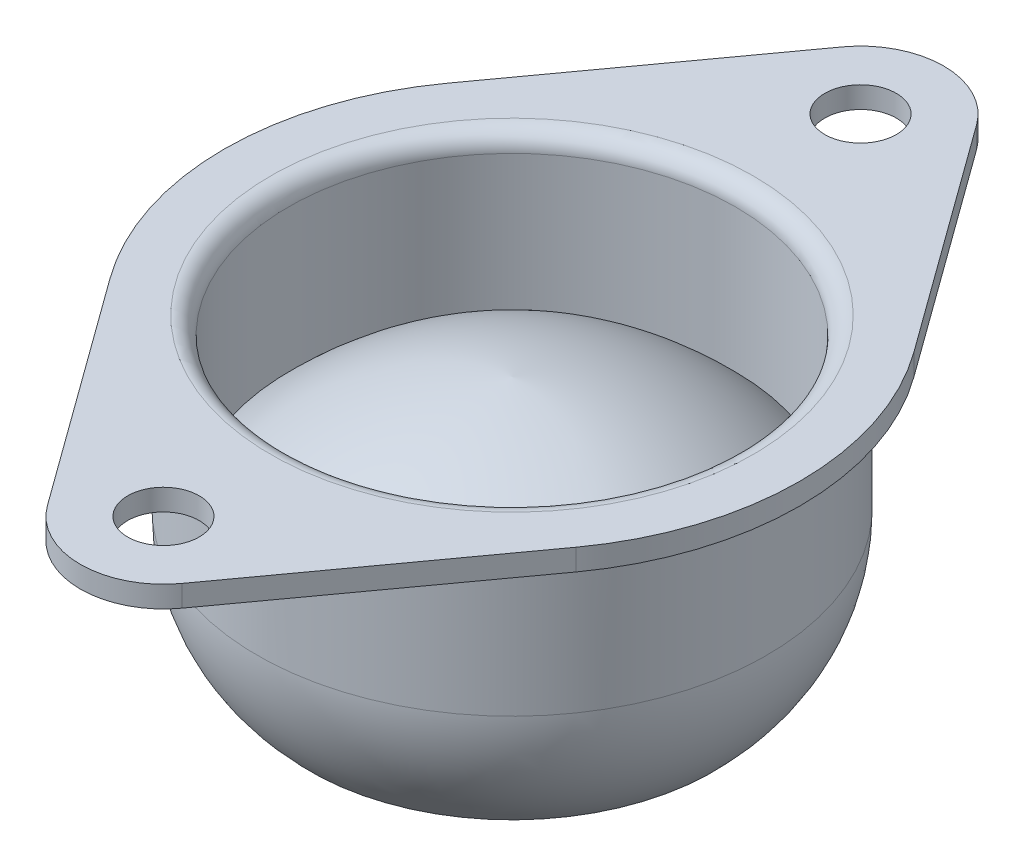
SolidWorks part; units mm, degrees
ref_plane "Plano frontal" through (0, 0, 0) normal (0, 0, 1) x (1, 0, 0)
ref_plane "Plano superior" through (0, 0, 0) normal (0, 1, 0) x (1, 0, 0)
ref_plane "Plano direito" through (0, 0, 0) normal (1, 0, 0) x (0, 0, -1)
sketch "Esboço1" plane through (0, 0, 0) normal (0, 0, 1) x (1, 0, 0)
  line L0 (0, 0) -> (0, 23844.2125) construction
  line L1 (0, 0) -> (-16.1, 0)
  line L2 (-16.1, 0) -> (-16.1, -1.2)
  line L3 (-16.1, -1.2) -> (-14.25, -1.2)
  line L4 (-14.25, -1.2) -> (-14.25, -9.3586)
  line L8 (0, 0) -> (0, -21)
  line L9 (0, -21) -> (9.18, -21) construction
  arc A3 (-14.25, -9.3586) -> (-11.25, -16.5) centre (-4.25, -9.3586) ccw
  arc A4 (-11.25, -16.5) -> (-7.5, -16) centre (-9.6827, -13.9419) ccw
  arc A5 (-7.5, -16) -> (0, -21) centre (0, -12.875) ccw
  dimension "D1" = 28.5
  dimension "D4" = 16.5
  dimension "D5" = 10
  dimension "D10" = 3
  dimension "D2" = 21
  dimension "D3" = 32.2
  dimension "D6" = 22.5
  dimension "D7" = 1.2
  dimension "D8" = 15
  dimension "D9" = 5
revolve "Revolução1" add sketch "Esboço1" angle 360 about L0
sketch "Esboço2" plane through (0, 0, 0) normal (0, 1, 0) x (1, 0, 0)
  line L0 (0, -19.5) -> (0, 19.5) construction
  line L1 (3.764, 22.2304) -> (13.0323, 9.4536)
  line L2 (-16.1, 0) -> (16.1, 0) construction
  line L3 (-3.764, 22.2304) -> (-13.0323, 9.4536)
  line L4 (3.764, -22.2304) -> (13.0323, -9.4536)
  line L5 (-3.764, -22.2304) -> (-13.0323, -9.4536)
  circle A2 centre (0, 0) radius 16.1 construction
  circle A3 centre (0, 0) radius 16.1
  circle A4 centre (0, -19.5) radius 2
  circle A5 centre (0, 19.5) radius 2
  arc A6 (3.764, 22.2304) -> (-3.764, 22.2304) centre (0, 19.5) ccw
  arc A7 (-3.764, -22.2304) -> (3.764, -22.2304) centre (0, -19.5) ccw
  point P0 (0, 24.15)
  point P4 (0, 0)
  point P6 (0, -24.15)
  point P15 (0, 0)
  dimension "D2" = 48.3
  dimension "D3" = 4
  dimension "D1" = 39
extrude "Ressalto-extrusão1" add sketch "Esboço2" against normal up to surface (1.2 mm away)
sketch "Esboço3" plane through (0, 0, 0) normal (1, 0, 0) x (0, 0, -1)
  line L0 (0, 0) -> (0, -27.9059) construction
  line L1 (-12.5, 0) -> (-12.5, -9)
  line L2 (-22.2304, 0) -> (-9.4536, 0) construction
  line L3 (-12.5, 0) -> (0, 0)
  line L4 (0, 0) -> (0, -3)
  arc A0 (-12.5, -9) -> (0, -3) centre (1.868, -22.9126) cw
  dimension "D1" = 25
  dimension "D4" = 20
  dimension "D2" = 9
  dimension "D3" = 3
revolve "Corte-Revolução1" cut sketch "Esboço3" angle 360 about L0
fillet "Filete1" radius 1 1 edges at (0, 0, 12.5)
fillet "Filete2" radius 1 1 edges at (0, -1.2, -14.25)
scale "Escala1" scale about centroid uniform scaling yes scale factor 0.571429
sketch "Esboço4" plane through (0, 0, 0) normal (0, 0, 1) x (1, 0, 0)
  line L1 (-9.2, -4.2127) -> (0, -4.2127)
  line L2 (-9.2, -4.2127) -> (-9.2, -16.2127)
  line L3 (-9.2, -16.2127) -> (0, -16.2127)
  line L4 (0, -4.2127) -> (0, -16.2127)
  arc A0 (-4.2857, -13.3556) -> (4.2857, -13.3556) centre (0, -11.5699) ccw construction
